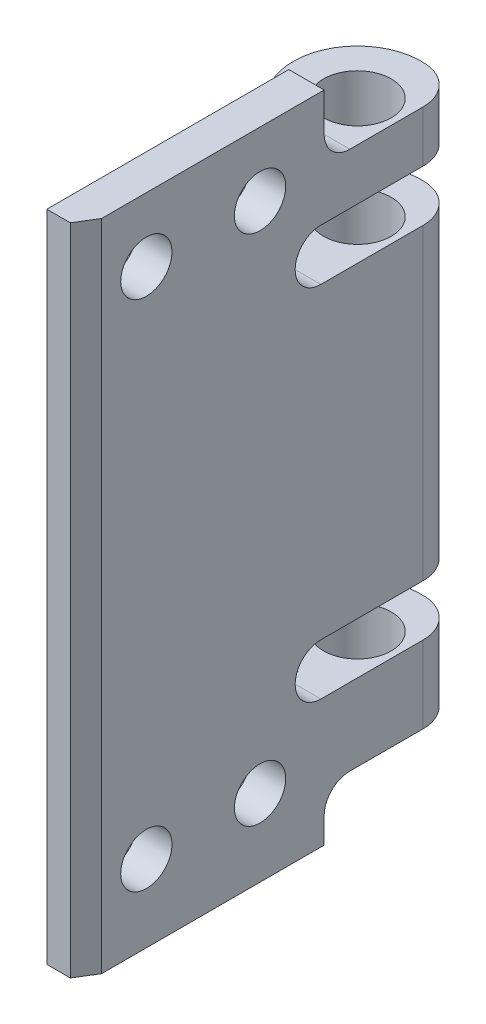
SolidWorks part; units mm, degrees
material "PLA"
ref_plane "Front Plane" through (0, 0, 0) normal (0, 0, 1) x (1, 0, 0)
ref_plane "Top Plane" through (0, 0, 0) normal (0, 1, 0) x (1, 0, 0)
ref_plane "Right Plane" through (0, 0, 0) normal (1, 0, 0) x (0, 0, -1)
ref_plane "Plane1" through (57.1966, 0, 0) normal (-1, 0, 0) x (0, -1, 0)
sketch "Sketch17" plane through (57.1966, 0, 0) normal (-1, 0, 0) x (0, -1, 0)
  line L0 (-38, -27.6338) -> (-14, -27.6338)
  line L1 (-10, -27.6338) -> (-10, -9.0284)
  line L2 (-10, -9.0284) -> (-42, -9.0284)
  line L3 (-42, -9.0284) -> (-42, -27.6338)
  arc A0 (-14, -27.6338) -> (-10, -27.6338) centre (-12, -27.6338) cw
  arc A1 (-42, -27.6338) -> (-38, -27.6338) centre (-40, -27.6338) cw
extrude "Boss-Extrude5" add sketch "Sketch17" against normal blind 2.76
chamfer "Chamfer1" distance 1.5104 angle 31.513 1 edges at (59.9567, 26, -9.0284)
ref_plane "Plane2" through (0, 38, 0) normal (0, 1, 0) x (1, 0, 0)
sketch "Sketch18" plane through (0, 38, 0) normal (0, 1, 0) x (1, 0, 0)
  line L0 (57.1966, 27.6338) -> (59.9567, 27.6338)
  line L1 (59.9567, 27.6338) -> (59.9567, 37.5187)
  line L2 (57.1966, 28.64) -> (57.1966, 27.6338)
  arc A0 (59.9567, 37.5187) -> (57.1966, 28.64) centre (56.819, 33.6257) ccw
extrude "Boss-Extrude6" add sketch "Sketch18" against normal blind 24
ref_plane "Plane3" through (0, 35, 0) normal (0, 1, 0) x (1, 0, 0)
sketch "Sketch19" plane through (0, 35, 0) normal (0, 1, 0) x (1, 0, 0)
  line L0 (57.1966, 15.8804) -> (57.1966, 23.2078)
  arc A0 (55.5117, 21.7521) -> (55.5117, 17.7521) centre (55.5117, 19.7521) ccw
  spline S0 degree 2 poles (57.1966, 15.8804) (56.9099, 17.3168) (55.5117, 17.7521) knots 0 0 0 1 1 1
  spline S1 degree 2 poles (55.5117, 21.7521) (56.7322, 22.0656) (57.1966, 23.2078) knots 0 0 0 1 1 1
extrude "Boss-Extrude7" add sketch "Sketch19" against normal blind 5
sketch "Sketch20" plane through (0, 10, 0) normal (0, -1, 0) x (1, 0, 0)
  line L0 (57.1966, -28.64) -> (57.1966, -9.0284)
  line L1 (57.1966, -9.0284) -> (59.0306, -9.0284)
  line L2 (59.0306, -9.0284) -> (59.9567, -10.5387)
  line L3 (59.9567, -10.5387) -> (59.9567, -37.5187)
  arc A0 (59.9567, -37.5187) -> (57.1966, -28.64) centre (56.819, -33.6257) cw
extrude "Boss-Extrude8" add sketch "Sketch20" along normal blind 6
sketch "Sketch21" plane through (0, 4, 0) normal (0, -1, 0) x (1, 0, 0)
  line L0 (57.1966, -27.8951) -> (57.1966, -9.0284)
  line L1 (57.1966, -9.0284) -> (59.0306, -9.0284)
  line L2 (59.0306, -9.0284) -> (59.9567, -10.5387)
  line L3 (59.9567, -10.5387) -> (59.9567, -27.8951)
  line L4 (59.9567, -27.8951) -> (59.9567, -28.64)
  line L5 (59.9567, -28.64) -> (59.9567, -37.5187)
  line L6 (59.9567, -37.5187) -> (57.1966, -37.5187)
  line L7 (57.1966, -37.5187) -> (57.1966, -28.64)
  line L8 (57.1966, -28.64) -> (57.1966, -27.8951)
extrude "Boss-Extrude9" add sketch "Sketch21" along normal blind 4
ref_plane "Plane4" through (0, 0, -37.5187) normal (0, 0, -1) x (-1, 0, 0)
sketch "Sketch28" plane through (0, 0, -37.5187) normal (0, 0, -1) x (-1, 0, 0)
  line L0 (-57.1966, 0) -> (-57.1966, 4)
  line L1 (-57.1966, 4) -> (-59.9567, 4)
  line L2 (-59.9567, 4) -> (-59.9567, 0)
  line L3 (-59.9567, 0) -> (-57.1966, 0)
extrude "Cut-Extrude3" cut sketch "Sketch28" against normal blind 8.8787
ref_plane "Plane5" through (0, 42, 0) normal (0, 1, 0) x (1, 0, 0)
sketch "Sketch36" plane through (0, 42, 0) normal (0, 1, 0) x (1, 0, 0)
  line L0 (59.9567, 37.5187) -> (59.9567, 10.5387)
  line L1 (59.9567, 10.5387) -> (59.0306, 9.0284)
  line L2 (59.0306, 9.0284) -> (57.1966, 9.0284)
  line L3 (57.1966, 9.0284) -> (57.1966, 28.64)
  arc A0 (57.1966, 28.64) -> (59.9567, 37.5187) centre (56.819, 33.6257) cw
extrude "Boss-Extrude10" add sketch "Sketch36" along normal blind 4
ref_plane "Plane6" through (0, 0, -28.64) normal (0, 0, -1) x (-1, 0, 0)
sketch "Sketch45" plane through (0, 0, -28.64) normal (0, 0, -1) x (-1, 0, 0)
  line L0 (-57.1966, 0) -> (-57.1966, 4)
  line L1 (-57.1966, 4) -> (-59.9567, 4)
  line L2 (-59.9567, 4) -> (-59.9567, 0)
  line L3 (-59.9567, 0) -> (-57.1966, 0)
extrude "Cut-Extrude4" cut sketch "Sketch45" against normal blind 0.7448
ref_plane "Plane7" through (0, 46, 0) normal (0, 1, 0) x (1, 0, 0)
sketch "Sketch55" plane through (0, 46, 0) normal (0, 1, 0) x (1, 0, 0)
  line L0 (59.9567, 10.5387) -> (59.0306, 9.0284)
  line L1 (59.0306, 9.0284) -> (57.1966, 9.0284)
  line L2 (57.1966, 9.0284) -> (57.1966, 27.8951)
  line L3 (57.1966, 27.8951) -> (59.9567, 27.8951)
  line L4 (59.9567, 27.8951) -> (59.9567, 10.5387)
extrude "Boss-Extrude11" add sketch "Sketch55" along normal blind 5
hole_wizard "Ø4.0 (4) Diameter Hole2" positions "Sketch57" profile "Sketch56" hole size "Ø4.0" standard "ANSI Metric"
sketch "Sketch57" plane through (57.1966, 0, 0) normal (-1, 0, 0) x (0, 0, 1)
  point P0 (-22.8951, 6)
  point P1 (-14.0284, 6)
  point P2 (-14.0284, 46)
  point P3 (-22.8951, 46)
sketch "Sketch56" plane through (57.1966, 6, -22.8951) normal (0, 1, 0) x (0, 0, 1)
  line L0 (0, 0) -> (0, 2.76)
  line L1 (0, 2.76) -> (2, 2.76)
  line L2 (2, 2.76) -> (2, 0)
  line L5 (2, 0) -> (0, 0)
  line L11 (0, -6.35) -> (0, 107.95) construction
  dimension "Thru Hole Dia." = 4
  dimension "Thru Hole Depth" = 2.76
hole_wizard "Hole4" positions "Sketch59" profile "Sketch58" legacy
sketch "Sketch59" plane through (0, 10, 0) normal (0, 1, 0) x (1, 0, 0)
  point P0 (56.819, 33.6257)
sketch "Sketch58" plane through (56.819, 10, -33.6257) normal (1, 0, 0) x (0, 0, 1)
  line L0 (0, 0) -> (0, 10)
  line L1 (0, 10) -> (2.6375, 10)
  line L2 (2.6375, 10) -> (2.6375, 0)
  line L3 (2.6375, 0) -> (0, 0)
  line L4 (0, 110) -> (0, -10) construction
  dimension "Diameter" = 5.275
  dimension "Depth" = 10
hole_wizard "Hole5" positions "Sketch61" profile "Sketch60" legacy
sketch "Sketch61" plane through (0, 38, 0) normal (0, 1, 0) x (1, 0, 0)
  point P0 (56.819, 33.6257)
sketch "Sketch60" plane through (56.819, 38, -33.6257) normal (1, 0, 0) x (0, 0, 1)
  line L0 (0, 0) -> (0, 38)
  line L1 (0, 38) -> (2.6375, 38)
  line L2 (2.6375, 38) -> (2.6375, 0)
  line L3 (2.6375, 0) -> (0, 0)
  line L4 (0, 110) -> (0, -10) construction
  dimension "Diameter" = 5.275
  dimension "Depth" = 38
hole_wizard "Hole6" positions "Sketch63" profile "Sketch62" legacy
sketch "Sketch63" plane through (0, 46, 0) normal (0, 1, 0) x (1, 0, 0)
  point P0 (56.819, 33.6257)
sketch "Sketch62" plane through (56.819, 46, -33.6257) normal (1, 0, 0) x (0, 0, 1)
  line L0 (0, 0) -> (0, 46)
  line L1 (0, 46) -> (2.6375, 46)
  line L2 (2.6375, 46) -> (2.6375, 0)
  line L3 (2.6375, 0) -> (0, 0)
  line L4 (0, 110) -> (0, -10) construction
  dimension "Diameter" = 5.275
  dimension "Depth" = 46
hole_wizard "Ø3.0 (3) Diameter Hole2" positions "Sketch65" profile "Sketch64" hole size "Ø3.0" standard "ANSI Metric"
sketch "Sketch65" plane through (0, 35, 0) normal (0, 1, 0) x (1, 0, 0)
  point P0 (55.5117, 19.7521)
sketch "Sketch64" plane through (55.5117, 35, -19.7521) normal (1, 0, 0) x (0, 0, 1)
  line L0 (0, 0) -> (0, 35)
  line L1 (0, 35) -> (1.5, 35)
  line L2 (1.5, 35) -> (1.5, 0)
  line L5 (1.5, 0) -> (0, 0)
  line L11 (0, -6.35) -> (0, 107.95) construction
  dimension "Thru Hole Dia." = 3
  dimension "Thru Hole Depth" = 35
fillet "Fillet3" radius 2 3 edges at (58.5767, 46, -27.8951) (58.5767, 4, -27.8951) (57.1966, 26, -28.64)
fillet "Fillet4" radius 3 3 edges at (59.9567, 26, -37.5187) (59.9567, 7, -37.5187) (59.9567, 44, -37.5187)
